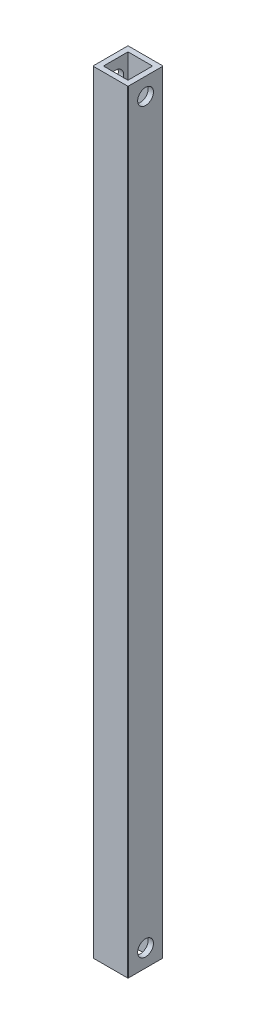
SolidWorks part; units mm, degrees
ref_plane "Front Plane" through (0, 0, 0) normal (0, 0, 1) x (1, 0, 0)
ref_plane "Top Plane" through (0, 0, 0) normal (0, 1, 0) x (1, 0, 0)
ref_plane "Right Plane" through (0, 0, 0) normal (1, 0, 0) x (0, 0, -1)
sketch "Sketch1" plane through (0, 0, 0) normal (0, 1, 0) x (1, 0, 0)
  line L1 (5, -5) -> (-5, -5)
  line L2 (5, -5) -> (5, 5)
  line L3 (5, 5) -> (-5, 5)
  line L4 (-5, -5) -> (-5, 5)
  line L5 (5, -5) -> (-5, 5) construction
  line L6 (5, 5) -> (-5, -5) construction
  point P0 (0, 0)
  dimension "D1" = 10
extrude "Extrude-Thin1" add sketch "Sketch1" along normal blind 220 thin
sketch "Sketch2" plane through (0, 0, 0) normal (1, 0, 0) x (0, 0, -1)
  line L0 (-5, 110) -> (-50005, 110) construction
  line L1 (-5, 220) -> (-5, 0) construction
  line L2 (0, 0) -> (0, 50000) construction
  line L3 (-5, 220) -> (5, 220) construction
  line L4 (0, 220) -> (0, -49780) construction
  circle A0 centre (0, 215) radius 2.25
  circle A1 centre (0, 5) radius 2.25
  point P4 (-5, 110)
  dimension "D1" = 4.5
  dimension "D2" = 5
extrude "Cut-Extrude1" cut sketch "Sketch2" against normal through all both and the other way through all
fillet "Fillet1" radius 0.2 4 edges at (-5, 110, 5) (5, 110, 5) (-5, 110, -5) (5, 110, -5)
sketch "Sketch3" plane through (0, 0, 0) normal (1, 0, 0) x (0, 0, -1)
  line L0 (-4.8, 110) -> (5, 110) construction
  line L1 (-4.8, 220) -> (-4.8, 0) construction
  line L2 (5, 220) -> (5, 0) construction
  circle A0 centre (0.1, 110) radius 4
  dimension "D1" = 8
extrude "Boss-Extrude1" [suppressed] add sketch "Sketch3" along normal mid plane 30
sketch "Sketch4" [suppressed] plane through (15, 0, 0) normal (1, 0, 0) x (0, 0, -1)
  circle A2 centre (0.1, 110) radius 4.5
  circle A3 centre (0.1, 110) radius 4.5
  dimension "D1" = 0.5
extrude "Boss-Extrude2" [suppressed] add sketch "Sketch4" against normal blind 1.5
fillet "Fillet2" [suppressed] radius 0.5
fillet "Fillet3" [suppressed] radius 0.5
mirror "Mirror1" [suppressed] about plane through (0, 0, 0) normal (1, 0, 0)
fillet "Fillet4" [suppressed] radius 0.5
ref_plane "Plane1" [suppressed] through (-12, 0, 0) normal (-1, 0, 0) x (0, 0, 1)
sketch "Sketch5" [suppressed] plane through (-12, 0, 0) normal (-1, 0, 0) x (0, 0, 1)
  point P0 (-0.1, 110)
  point P3 (-0.1, 101)
  dimension "D1" = 9
ref_plane "Plane2" [suppressed] through (12, 0, 0) normal (1, 0, 0) x (0, 0, -1)
sketch "Sketch6" [suppressed] plane through (12, 0, 0) normal (1, 0, 0) x (0, 0, -1)
  point P0 (0.1, 110)
  point P1 (0.1, 101)
  dimension "D1" = 9
